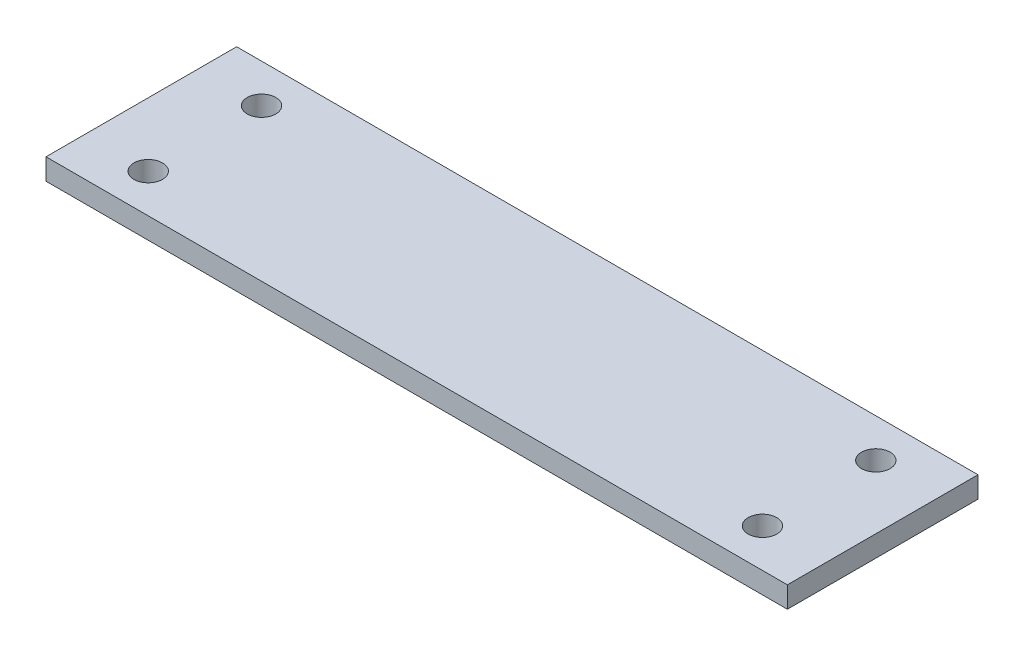
SolidWorks part; units mm, degrees
ref_plane "Front Plane" through (0, 0, 0) normal (0, 0, 1) x (1, 0, 0)
ref_plane "Top Plane" through (0, 0, 0) normal (0, 1, 0) x (1, 0, 0)
ref_plane "Right Plane" through (0, 0, 0) normal (1, 0, 0) x (0, 0, -1)
sketch "Sketch3" plane through (0, 0, 0) normal (0, 1, 0) x (1, 0, 0)
  line L5 (-29, 5.35) -> (29, 5.35)
  line L6 (-29, 5.35) -> (-29, -5.35)
  line L7 (-29, -5.35) -> (29, -5.35)
  line L8 (29, 5.35) -> (29, -5.35)
  line L9 (0, -5.35) -> (0, 5.35) construction
  line L10 (-29, 0) -> (29, 0) construction
  line L11 (-35, 9) -> (35, 9)
  line L12 (-35, 9) -> (-35, -9)
  line L13 (-35, -9) -> (35, -9)
  line L14 (35, 9) -> (35, -9)
  line L15 (0, -9) -> (0, 9) construction
  line L16 (-35, 0) -> (35, 0) construction
  circle A0 centre (-29, 5.35) radius 1.35
  circle A1 centre (29, 5.35) radius 1.35
  circle A2 centre (29, -5.35) radius 1.35
  circle A3 centre (-29, -5.35) radius 1.35
  point P0 (0, 0)
  point P9 (0, 0)
  dimension "D3" = 2.7
  dimension "D4" = 2.7
  dimension "D5" = 2.7
  dimension "D6" = 2.7
  dimension "D1" = 10.7
  dimension "D2" = 58
  dimension "D7" = 70
  dimension "D8" = 18
extrude "Boss-Extrude1" add sketch "Sketch3" along normal blind 2 contours L14 L11 L12 L13 A3 L6 A0 L5 A1 L8 A2 L7 | A3 L7 A2 L8 A1 L5 A0 L6
